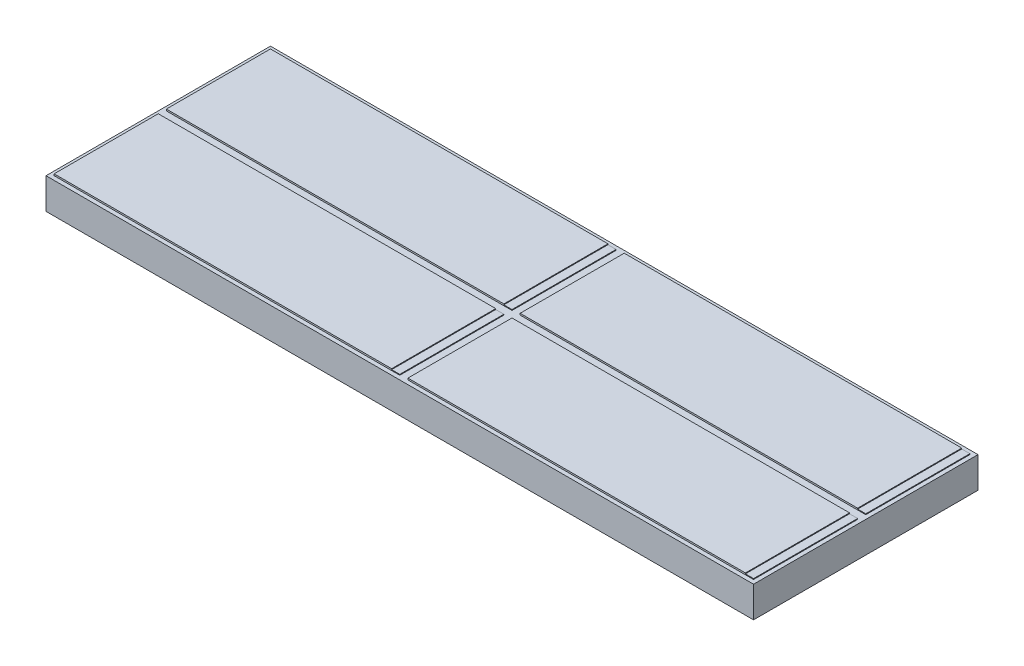
SolidWorks part; units mm, degrees
ref_plane "Front Plane" through (0, 0, 0) normal (0, 0, 1) x (1, 0, 0)
ref_plane "Top Plane" through (0, 0, 0) normal (0, 1, 0) x (1, 0, 0)
ref_plane "Right Plane" through (0, 0, 0) normal (1, 0, 0) x (0, 0, -1)
sketch "Sketch1" plane through (0, 0, 0) normal (0, 1, 0) x (1, 0, 0)
  line L1 (-11.2978, 9.8192) -> (32.2022, 9.8192)
  line L2 (-11.2978, 9.8192) -> (-11.2978, -3.9808)
  line L3 (-11.2978, -3.9808) -> (32.2022, -3.9808)
  line L4 (32.2022, 9.8192) -> (32.2022, -3.9808)
  dimension "D1" = 13.8
  dimension "D2" = 43.5
extrude "Boss-Extrude1" add sketch "Sketch1" along normal blind 1.9 contours L2 L3 L4 L1
sketch "Sketch2" plane through (0, 1.9, 0) normal (0, 1, 0) x (1, 0, 0)
  line L0 (-11.2978, 2.9192) -> (32.2022, 2.9192) construction
  line L1 (-11.2978, 9.8192) -> (-11.2978, -3.9808) construction
  line L2 (32.2022, 9.8192) -> (32.2022, -3.9808) construction
  line L3 (10.4522, 9.8192) -> (10.4522, -3.9808) construction
  line L4 (-11.2978, 9.8192) -> (32.2022, 9.8192) construction
  line L5 (-11.2978, -3.9808) -> (32.2022, -3.9808) construction
  line L6 (10.2022, -3.7308) -> (10.2022, 2.6692)
  line L7 (-11.0478, 9.5692) -> (10.2022, 9.5692)
  line L8 (-11.0478, 9.5692) -> (-11.0478, 3.1692)
  line L9 (-11.0478, 3.1692) -> (10.2022, 3.1692)
  line L10 (10.2022, 9.5692) -> (10.2022, 3.1692)
  line L11 (-11.0478, -3.7308) -> (10.2022, -3.7308)
  line L12 (-11.0478, -3.7308) -> (-11.0478, 2.6692)
  line L13 (-11.0478, 2.6692) -> (10.2022, 2.6692)
  line L14 (31.9522, 3.1692) -> (10.7022, 3.1692)
  line L15 (31.9522, 9.5692) -> (31.9522, 3.1692)
  line L16 (31.9522, 9.5692) -> (10.7022, 9.5692)
  line L17 (10.7022, 9.5692) -> (10.7022, 3.1692)
  line L18 (31.9522, -3.7308) -> (10.7022, -3.7308)
  line L19 (31.9522, -3.7308) -> (31.9522, 2.6692)
  line L20 (31.9522, 2.6692) -> (10.7022, 2.6692)
  line L21 (10.7022, -3.7308) -> (10.7022, 2.6692)
  dimension "D1" = 0.25
  dimension "D2" = 0.25
  dimension "D3" = 0.25
  dimension "D4" = 0.25
extrude "Boss-Extrude2" add sketch "Sketch2" along normal blind 0.1
sketch "Sketch10" plane through (0, 2, 0) normal (0, 1, 0) x (1, 0, 0)
  line L0 (10.2022, 2.6692) -> (-11.0478, 2.6692) construction
  line L1 (10.2022, -3.7308) -> (9.7022, -3.7308)
  line L2 (10.2022, -3.7308) -> (10.2022, 2.6692)
  line L3 (10.2022, 2.6692) -> (9.7022, 2.6692)
  line L4 (9.7022, -3.7308) -> (9.7022, 2.6692)
  line L5 (31.9522, 9.5692) -> (10.7022, 9.5692) construction
  line L6 (31.9522, -3.7308) -> (31.4522, -3.7308)
  line L7 (31.9522, -3.7308) -> (31.9522, 2.6692)
  line L8 (31.9522, 2.6692) -> (31.4522, 2.6692)
  line L9 (31.4522, -3.7308) -> (31.4522, 2.6692)
  line L10 (10.2022, 3.1692) -> (9.7022, 3.1692)
  line L11 (10.2022, 3.1692) -> (10.2022, 9.5692)
  line L12 (10.2022, 9.5692) -> (9.7022, 9.5692)
  line L13 (9.7022, 3.1692) -> (9.7022, 9.5692)
  line L14 (31.9522, 3.1692) -> (31.4522, 3.1692)
  line L15 (31.9522, 3.1692) -> (31.9522, 9.5692)
  line L16 (31.9522, 9.5692) -> (31.4522, 9.5692)
  line L17 (31.4522, 3.1692) -> (31.4522, 9.5692)
  line L18 (10.2022, 9.5692) -> (-11.0478, 9.5692) construction
  dimension "D1" = 0.5
  dimension "D2" = 0.5
  dimension "D3" = 0.5
  dimension "D4" = 0.5
extrude "Cut-Extrude1" cut sketch "Sketch10" against normal blind 0.05
